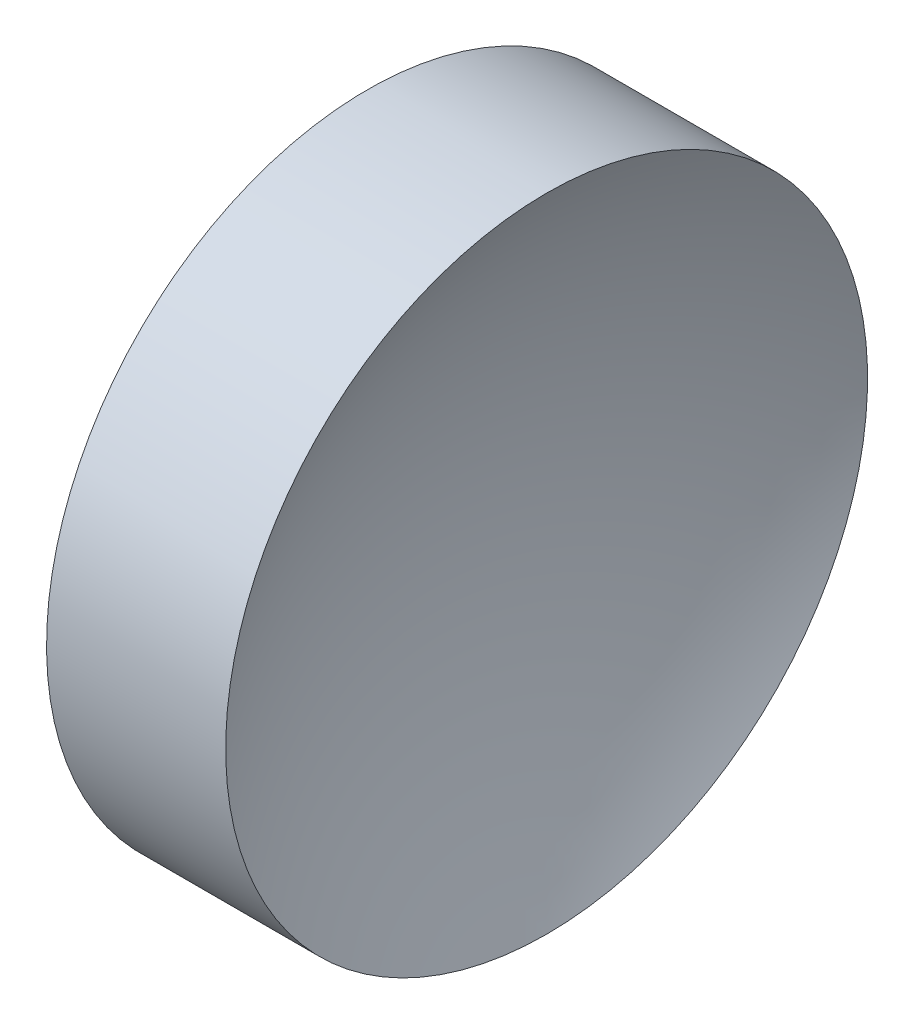
SolidWorks part; units mm, degrees
ref_plane "前视基准面" through (0, 0, 0) normal (0, 0, 1) x (1, 0, 0)
ref_plane "上视基准面" through (0, 0, 0) normal (0, 1, 0) x (1, 0, 0)
ref_plane "右视基准面" through (0, 0, 0) normal (1, 0, 0) x (0, 0, -1)
sketch "草图1" plane through (0, 0, 0) normal (0, 0, 1) x (1, 0, 0)
  line L0 (21.506, 13.0311) -> (26.997, 13.0311) construction
  line L1 (22.4242, 13.0311) -> (22.4242, 18.0311)
  line L2 (22.4242, 18.0311) -> (25.2149, 18.0311)
  line L3 (23.9242, 13.0311) -> (22.4242, 13.0311)
  arc A0 (25.2149, 18.0311) -> (23.9242, 13.0311) centre (34.2542, 13.0311) ccw
revolve "旋转1" add sketch "草图1" angle 360 about L0
